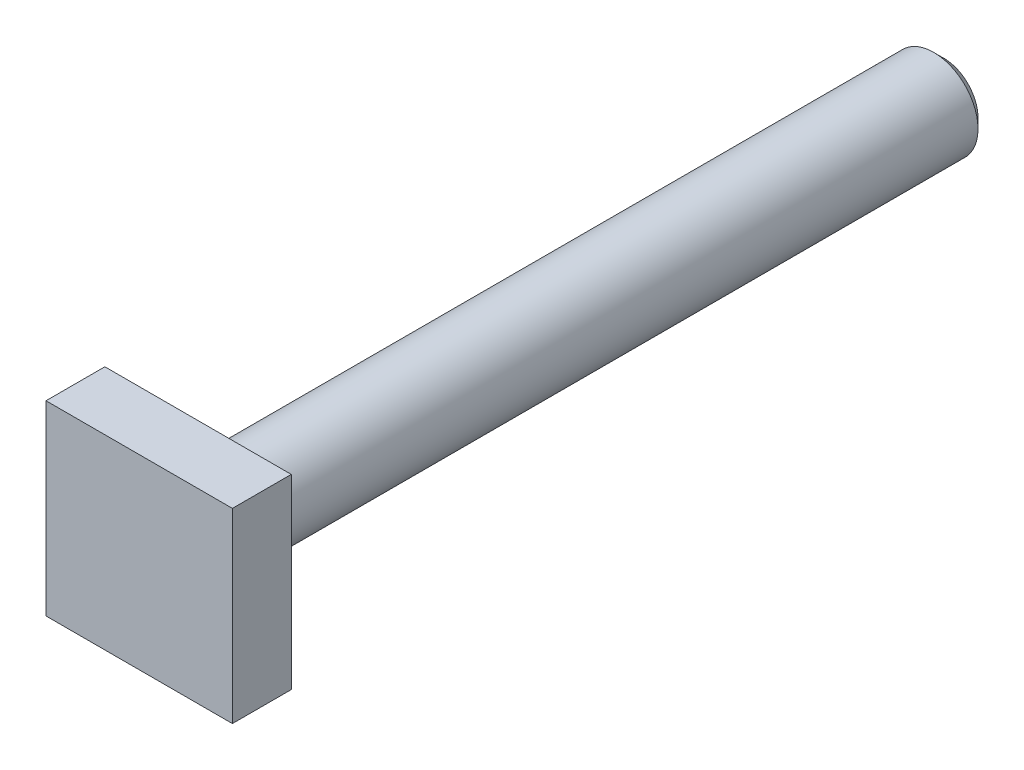
SolidWorks part; units mm, degrees
ref_plane "Front Plane" through (0, 0, 0) normal (0, 0, 1) x (1, 0, 0)
ref_plane "Top Plane" through (0, 0, 0) normal (0, 1, 0) x (1, 0, 0)
ref_plane "Right Plane" through (0, 0, 0) normal (1, 0, 0) x (0, 0, -1)
sketch "Sketch1" plane through (0, 0, 0) normal (0, 0, 1) x (1, 0, 0)
  line L1 (-9.5, 9.5) -> (9.5, 9.5)
  line L2 (-9.5, 9.5) -> (-9.5, -9.5)
  line L3 (-9.5, -9.5) -> (9.5, -9.5)
  line L4 (9.5, 9.5) -> (9.5, -9.5)
  line L5 (-9.5, 9.5) -> (9.5, -9.5) construction
  line L6 (-9.5, -9.5) -> (9.5, 9.5) construction
  point P0 (0, 0)
  dimension "D1" = 19
  dimension "D2" = 19
extrude "Boss-Extrude1" add sketch "Sketch1" against normal blind 6
sketch "Sketch2" plane through (0, 0, -6) normal (0, 0, -1) x (-1, 0, 0)
  circle A0 centre (0, 0) radius 4.5
  dimension "D1" = 9
extrude "Boss-Extrude2" add sketch "Sketch2" along normal blind 76
chamfer "Chamfer1" distance 1 angle 45 1 edges at (-4.5, 0, -82)
